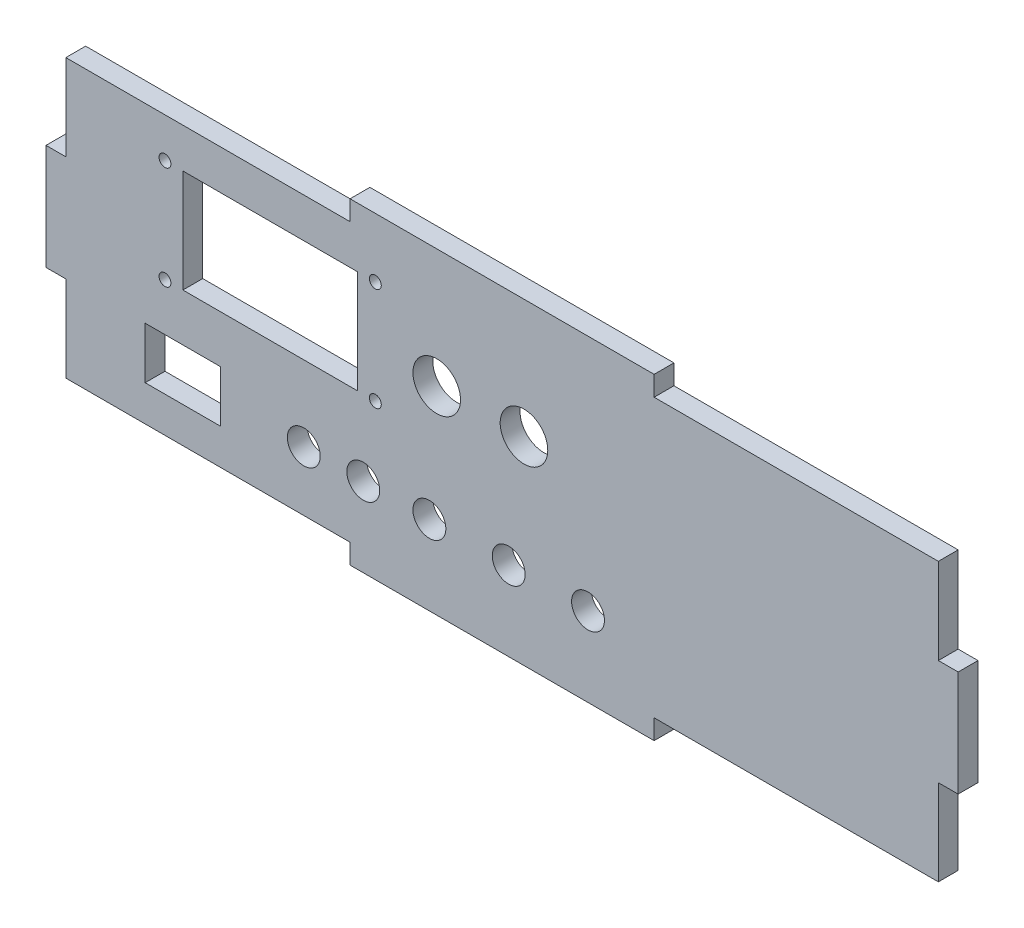
SolidWorks part; units mm, degrees
ref_plane "Alzado" through (0, 0, 0) normal (0, 0, 1) x (1, 0, 0)
ref_plane "Planta" through (0, 0, 0) normal (0, 1, 0) x (1, 0, 0)
ref_plane "Vista lateral" through (0, 0, 0) normal (1, 0, 0) x (0, 0, -1)
sketch "Croquis1" plane through (0, 0, 0) normal (0, 0, 1) x (1, 0, 0)
  line L0 (30, 65) -> (83.04, 65) construction
  line L1 (0, 0) -> (230, 0)
  line L2 (0, 0) -> (0, 80)
  line L3 (0, 80) -> (230, 80)
  line L4 (230, 0) -> (230, 80)
  line L5 (83.04, 65) -> (83.04, 39) construction
  line L6 (83.04, 39) -> (30, 39) construction
  line L7 (30, 39) -> (30, 65) construction
  line L8 (0, 40) -> (-6.7015, 40) construction
  line L9 (0, 53.3333) -> (5, 53.3333)
  line L10 (0, 53.3333) -> (0, 26.6667)
  line L11 (0, 26.6667) -> (5, 26.6667)
  line L12 (5, 53.3333) -> (5, 26.6667)
  line L13 (76.6667, 80) -> (153.3333, 80)
  line L14 (76.6667, 80) -> (76.6667, 75)
  line L15 (76.6667, 75) -> (153.3333, 75)
  line L16 (153.3333, 80) -> (153.3333, 75)
  line L17 (115, 80) -> (115, 87.6964) construction
  line L18 (230, 26.6667) -> (225, 26.6667)
  line L19 (230, 53.3333) -> (225, 53.3333)
  line L20 (225, 53.3333) -> (225, 26.6667)
  line L21 (153.3333, 0) -> (153.3333, 5)
  line L22 (76.6667, 0) -> (76.6667, 5)
  line L23 (76.6667, 5) -> (153.3333, 5)
  line L24 (56.52, 65) -> (56.52, 39) construction
  line L25 (30, 52) -> (83.04, 52) construction
  line L26 (76.6667, 75) -> (0, 75)
  line L27 (34.52, 65) -> (78.52, 65)
  line L28 (34.52, 65) -> (34.52, 39)
  line L29 (34.52, 39) -> (78.52, 39)
  line L30 (78.52, 65) -> (78.52, 39)
  line L31 (34.52, 65) -> (78.52, 39) construction
  line L32 (34.52, 39) -> (78.52, 65) construction
  line L33 (153.3333, 75) -> (230, 75)
  line L34 (5, 0) -> (5, 80)
  line L35 (0, 5) -> (230, 5)
  line L36 (225, 0) -> (225, 80)
  circle A0 centre (30, 65) radius 1.5
  circle A1 centre (83.04, 65) radius 1.5
  circle A2 centre (30, 39) radius 1.5
  circle A3 centre (83.04, 39) radius 1.5
  point P37 (56.52, 52)
  dimension "D3" = 3
  dimension "D1" = 80
  dimension "D2" = 230
  dimension "D4" = 53.04
  dimension "D5" = 26
  dimension "D6" = 30
  dimension "D7" = 15
  dimension "D8" = 26.6667
  dimension "D9" = 26.6667
  dimension "D10" = 76.6667
  dimension "D11" = 76.6667
  dimension "D12" = 5
  dimension "D13" = 5
  dimension "D15" = 26
  dimension "D14" = 44
extrude "Saliente-Extruir1" add sketch "Croquis1" along normal blind 5 contours L35 L36 L20 L33 L15 L26 L34 L12 L23 A3 A2 A1 A0 L27 L30 L29 L28 | L19 L20 L18 L4 | L23 L22 L1 L21 | L12 L9 L2 L11 | L16 L3 L14 L15
sketch "Croquis2" plane through (0, 0, 5) normal (0, 0, 1) x (1, 0, 0)
  line L0 (96.6667, 20) -> (116.6667, 20) construction
  line L3 (116.6667, 20) -> (136.6667, 20) construction
  line L5 (76.6667, 0) -> (76.6667, 5) construction
  line L6 (153.3333, 5) -> (225, 5) construction
  circle A0 centre (96.6667, 20) radius 4.15
  circle A1 centre (116.6667, 20) radius 4.15
  circle A2 centre (136.6667, 20) radius 4.15
  point P4 (126.6667, 20)
  dimension "D1" = 8.3
  dimension "D2" = 15
  dimension "D3" = 20
  dimension "D4" = 20
  dimension "D5" = 20
extrude "Cortar-Extruir1" cut sketch "Croquis2" against normal blind 10
sketch "Croquis3" plane through (0, 0, 5) normal (0, 0, 1) x (1, 0, 0)
  line L0 (34.52, 39) -> (78.52, 39) construction
  line L1 (25, 27) -> (44, 27)
  line L2 (25, 27) -> (25, 14)
  line L3 (25, 14) -> (44, 14)
  line L4 (44, 27) -> (44, 14)
  line L6 (5, 5) -> (5, 26.6667) construction
  dimension "D1" = 19
  dimension "D2" = 13
  dimension "D3" = 12
  dimension "D4" = 20
extrude "Cortar-Extruir2" cut sketch "Croquis3" against normal blind 10
sketch "Croquis4" plane through (0, 0, 5) normal (0, 0, 1) x (1, 0, 0)
  line L0 (65, 20) -> (80, 20) construction
  line L3 (5, 53.3333) -> (5, 75) construction
  line L4 (5, 5) -> (76.6667, 5) construction
  circle A0 centre (65, 20) radius 4.15
  circle A1 centre (80, 20) radius 4.15
  dimension "D1" = 8.3
  dimension "D4" = 15
  dimension "D2" = 15
  dimension "D3" = 60
extrude "Cortar-Extruir3" cut sketch "Croquis4" against normal blind 10
sketch "Croquis5" plane through (0, 0, 5) normal (0, 0, 1) x (1, 0, 0)
  line L0 (98.52, 50) -> (120.52, 50) construction
  line L1 (34.52, 65) -> (78.52, 65) construction
  line L2 (78.52, 65) -> (78.52, 39) construction
  circle A0 centre (98.52, 50) radius 6
  circle A1 centre (120.52, 50) radius 6
  dimension "D1" = 12
  dimension "D2" = 12
  dimension "D3" = 22
  dimension "D4" = 15
  dimension "D5" = 20
extrude "Cortar-Extruir4" cut sketch "Croquis5" against normal blind 10
sketch "Croquis6" plane through (0, 0, 5) normal (0, 0, 1) x (1, 0, 0)
  line L0 (44, 14) -> (44, 27) construction
  line L1 (25, 14) -> (44, 14) construction
  line L2 (44, 27) -> (25, 27) construction
  line L3 (25, 27) -> (25, 14) construction
  line L4 (34.52, 39) -> (78.52, 39) construction
  line L5 (34.52, 65) -> (34.52, 39) construction
  line L6 (34.52, 65) -> (78.52, 65) construction
  line L7 (78.52, 65) -> (78.52, 39) construction
  line L8 (44, 14) -> (44, 27)
  line L9 (25, 14) -> (44, 14)
  line L10 (44, 27) -> (25, 27)
  line L11 (25, 27) -> (25, 14)
  line L12 (34.52, 39) -> (78.52, 39)
  line L13 (34.52, 65) -> (34.52, 39)
  line L14 (34.52, 65) -> (78.52, 65)
  line L15 (78.52, 65) -> (78.52, 39)
  line L20 (5, 5) -> (76.6667, 5)
  line L21 (76.6667, 5) -> (76.6667, 0)
  line L22 (76.6667, 0) -> (153.3333, 0)
  line L23 (153.3333, 0) -> (153.3333, 5)
  line L24 (153.3333, 5) -> (225, 5)
  line L25 (225, 5) -> (225, 26.6667)
  line L26 (225, 26.6667) -> (230, 26.6667)
  line L27 (230, 26.6667) -> (230, 53.3333)
  line L28 (230, 53.3333) -> (225, 53.3333)
  line L29 (225, 53.3333) -> (225, 75)
  line L30 (225, 75) -> (153.3333, 75)
  line L31 (153.3333, 75) -> (153.3333, 80)
  line L32 (153.3333, 80) -> (76.6667, 80)
  line L33 (76.6667, 80) -> (76.6667, 75)
  line L34 (76.6667, 75) -> (5, 75)
  line L35 (5, 75) -> (5, 53.3333)
  line L36 (5, 53.3333) -> (0, 53.3333)
  line L37 (0, 53.3333) -> (0, 26.6667)
  line L38 (0, 26.6667) -> (5, 26.6667)
  line L39 (5, 26.6667) -> (5, 5)
  line L40 (5, 5) -> (76.6667, 5)
  line L41 (76.6667, 5) -> (76.6667, 0)
  line L42 (76.6667, 0) -> (153.3333, 0)
  line L43 (153.3333, 0) -> (153.3333, 5)
  line L44 (153.3333, 5) -> (225, 5)
  line L45 (225, 5) -> (225, 26.6667)
  line L46 (225, 26.6667) -> (230, 26.6667)
  line L47 (230, 26.6667) -> (230, 53.3333)
  line L48 (230, 53.3333) -> (225, 53.3333)
  line L49 (225, 53.3333) -> (225, 75)
  line L50 (225, 75) -> (153.3333, 75)
  line L51 (153.3333, 75) -> (153.3333, 80)
  line L52 (153.3333, 80) -> (76.6667, 80)
  line L53 (76.6667, 80) -> (76.6667, 75)
  line L54 (76.6667, 75) -> (5, 75)
  line L55 (5, 75) -> (5, 53.3333)
  line L56 (5, 53.3333) -> (0, 53.3333)
  line L57 (0, 53.3333) -> (0, 26.6667)
  line L58 (0, 26.6667) -> (5, 26.6667)
  line L59 (5, 26.6667) -> (5, 5)
  circle A0 centre (98.52, 50) radius 6 construction
  circle A1 centre (120.52, 50) radius 6 construction
  circle A2 centre (136.6667, 20) radius 4.15 construction
  circle A3 centre (116.6667, 20) radius 4.15 construction
  circle A4 centre (96.6667, 20) radius 4.15 construction
  circle A5 centre (80, 20) radius 4.15 construction
  circle A6 centre (65, 20) radius 4.15 construction
  circle A7 centre (83.04, 65) radius 1.5 construction
  circle A8 centre (83.04, 39) radius 1.5 construction
  circle A9 centre (30, 39) radius 1.5 construction
  circle A10 centre (30, 65) radius 1.5 construction
  circle A11 centre (98.52, 50) radius 6
  circle A12 centre (120.52, 50) radius 6
  circle A13 centre (136.6667, 20) radius 4.15
  circle A14 centre (116.6667, 20) radius 4.15
  circle A15 centre (96.6667, 20) radius 4.15
  circle A16 centre (80, 20) radius 4.15
  circle A17 centre (65, 20) radius 4.15
  circle A18 centre (83.04, 65) radius 1.5
  circle A19 centre (83.04, 39) radius 1.5
  circle A20 centre (30, 39) radius 1.5
  circle A21 centre (30, 65) radius 1.5
  dimension "D1" = 0
